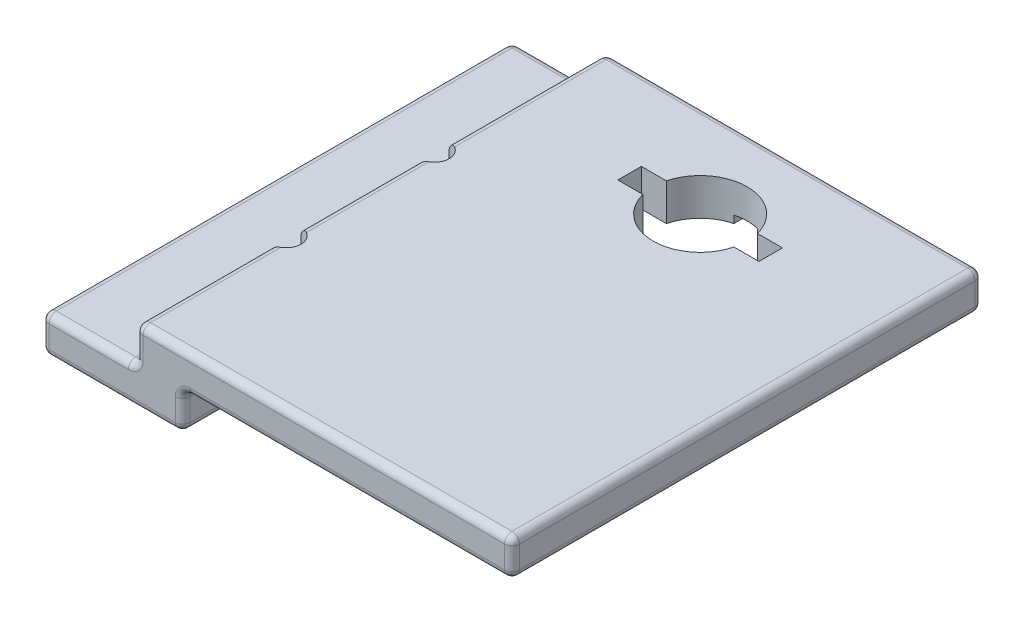
SolidWorks part; units mm, degrees
ref_plane "Front Plane" through (0, 0, 0) normal (0, 0, 1) x (1, 0, 0)
ref_plane "Top Plane" through (0, 0, 0) normal (0, 1, 0) x (1, 0, 0)
ref_plane "Right Plane" through (0, 0, 0) normal (1, 0, 0) x (0, 0, -1)
sketch "Sketch1" plane through (0, 0, 0) normal (0, 0, 1) x (1, 0, 0)
  line L1 (-31.75, 5) -> (31.75, 5)
  line L2 (-31.75, 5) -> (-31.75, -5)
  line L3 (-31.75, -5) -> (31.75, -5)
  line L4 (31.75, 5) -> (31.75, -5)
  line L5 (-31.75, 5) -> (31.75, -5) construction
  line L6 (-31.75, -5) -> (31.75, 5) construction
  point P0 (0, 0)
  dimension "D1" = 10
  dimension "D2" = 63.5
extrude "Boss-Extrude1" add sketch "Sketch1" along normal blind 63.5
sketch "Sketch2" plane through (0, 5, 0) normal (0, 1, 0) x (1, 0, 0)
  line L0 (31.75, -63.5) -> (-31.75, -63.5) construction
  line L1 (-31.75, 0) -> (-19.05, 0)
  line L2 (-31.75, 0) -> (-31.75, -63.5)
  line L3 (-31.75, -63.5) -> (-19.05, -63.5)
  line L4 (-19.05, 0) -> (-19.05, -63.5)
  dimension "D1" = 12.7
extrude "Cut-Extrude1" cut sketch "Sketch2" against normal offset from surface (5 mm away) 5 up to face at (0, -5, 31.75)
sketch "Sketch3" plane through (0, -5, 0) normal (0, -1, 0) x (1, 0, 0)
  line L0 (-31.75, 0) -> (31.75, 0) construction
  line L1 (31.75, 63.5) -> (-12.7, 63.5)
  line L2 (31.75, 63.5) -> (31.75, 0)
  line L3 (31.75, 0) -> (-12.7, 0)
  line L4 (-12.7, 63.5) -> (-12.7, 0)
  line L5 (-31.75, 63.5) -> (-31.75, 0) construction
  dimension "D1" = 19.05
extrude "Cut-Extrude2" cut sketch "Sketch3" against normal blind 5
sketch "Sketch4" plane through (0, 5, 0) normal (0, 1, 0) x (1, 0, 0)
  line L0 (6.35, 0) -> (6.35, -63.5) construction
  line L1 (31.75, -63.5) -> (-19.05, -63.5) construction
  line L2 (31.75, 0) -> (-19.05, 0) construction
  circle A0 centre (6.35, -12.7) radius 6.35
  dimension "D1" = 12.7
  dimension "D2" = 12.7
extrude "Cut-Extrude3" cut sketch "Sketch4" against normal blind 5
sketch "Sketch5" plane through (0, 0, 0) normal (0, -1, 0) x (1, 0, 0)
  line L1 (-3.175, 14.2875) -> (15.875, 14.2875)
  line L2 (-3.175, 14.2875) -> (-3.175, 11.1125)
  line L3 (-3.175, 11.1125) -> (15.875, 11.1125)
  line L4 (15.875, 14.2875) -> (15.875, 11.1125)
  line L5 (-3.175, 14.2875) -> (15.875, 11.1125) construction
  line L6 (-3.175, 11.1125) -> (15.875, 14.2875) construction
  point P0 (6.35, 12.7)
  dimension "D1" = 19.05
  dimension "D2" = 3.175
extrude "Cut-Extrude4" cut sketch "Sketch5" against normal blind 5
sketch "Sketch6" plane through (0, 0, 0) normal (0, 1, 0) x (1, 0, 0)
  line L0 (-31.75, 0) -> (-19.05, 0) construction
  line L1 (-31.75, -63.5) -> (-31.75, 0) construction
  circle A0 centre (-19.05, -43.18) radius 2
  circle A1 centre (-19.05, -23.18) radius 2
  dimension "D3" = 4
  dimension "D1" = 43.18
  dimension "D2" = 20
  dimension "D4" = 12.7
extrude "Cut-Extrude5" cut sketch "Sketch6" along normal through all
sketch "Sketch7" plane through (0, 0, 0) normal (0, 1, 0) x (1, 0, 0)
  circle A0 centre (-19.05, -23.18) radius 1.65
  circle A1 centre (-19.05, -43.18) radius 1.65
  dimension "D1" = 3.3
extrude "Cut-Extrude6" cut sketch "Sketch7" against normal through all
fillet "Fillet1" radius 1 28 edges at (-31.75, -5, 31.75) (-31.75, 0, 31.75) (31.75, 5, 31.75) (31.75, 0, 31.75) (31.75, 2.5, 0) (6.35, 5, 0) (-19.05, 2.5, 0) (-25.4, 0, 0) (-31.75, -2.5, 0) (-22.225, -5, 0) (9.525, 0, 0) (-22.225, -5, 63.5) (-31.75, -2.5, 63.5) (-25.4, 0, 63.5) (-19.05, 2.5, 63.5) (6.35, 5, 63.5) (31.75, 2.5, 63.5) (9.525, 0, 63.5) (-12.7, -2.5, 63.5) (-12.7, 0, 31.75) (-12.7, -2.5, 0) (-12.7, -5, 31.75) (-19.05, 5, 10.59) (-19.05, 0, 10.59) (-19.05, 5, 33.18) (-19.05, 0, 33.18) (-19.05, 0, 54.34) (-19.05, 5, 54.34)
sketch "Sketch8" plane through (0, 0, 0) normal (0, -1, 0) x (-1, 0, 0)
  line L1 (-4.76, -22.225) -> (-7.94, -22.225)
  line L2 (-4.76, -22.225) -> (-4.76, -3.175)
  line L3 (-4.76, -3.175) -> (-7.94, -3.175)
  line L4 (-7.94, -22.225) -> (-7.94, -3.175)
  line L5 (-4.76, -22.225) -> (-7.94, -3.175) construction
  line L6 (-4.76, -3.175) -> (-7.94, -22.225) construction
  point P0 (-6.35, -12.7)
  dimension "D1" = 19.05
  dimension "D2" = 3.18
extrude "Cut-Extrude7" cut sketch "Sketch8" against normal blind 1
